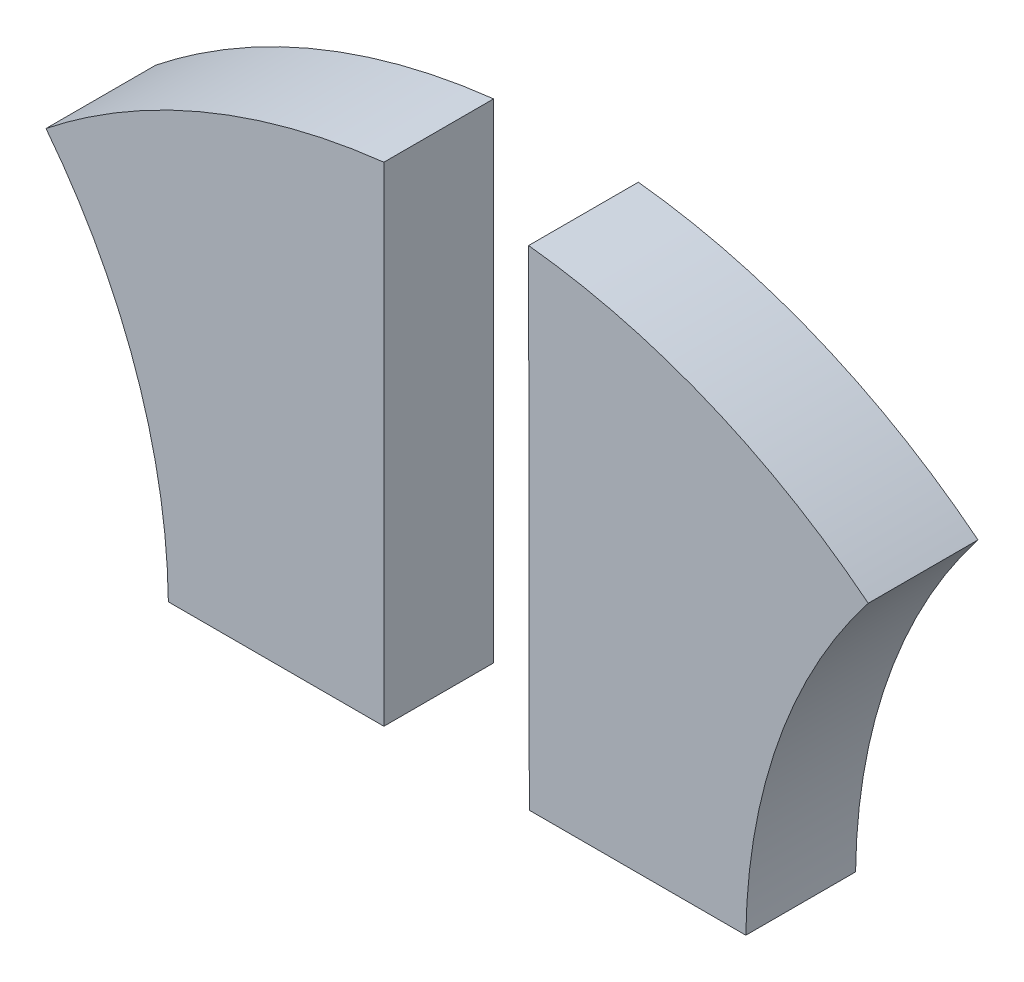
SolidWorks part; units mm, degrees
ref_plane "Alzado" through (0, 0, 0) normal (0, 0, 1) x (1, 0, 0)
ref_plane "Planta" through (0, 0, 0) normal (0, 1, 0) x (1, 0, 0)
ref_plane "Vista lateral" through (0, 0, 0) normal (1, 0, 0) x (0, 0, -1)
sketch "Model" plane through (0, 0, 0) normal (0, 0, 1) x (1, 0, 0)
  line L0 (34.3971, 11.0191) -> (28.5047, 11.0191)
  line L1 (34.3971, 24.3756) -> (34.3971, 11.0191)
  line L2 (44.2933, 11.0191) -> (38.3729, 11.0191)
  line L3 (38.3729, 11.0191) -> (38.3541, 24.3809)
  arc A0 (28.5047, 11.0191) -> (25.1591, 20.555) centre (12.6955, 10.8273) ccw
  arc A1 (47.6408, 20.5544) -> (44.2933, 11.0191) centre (60.0956, 10.8267) ccw
  ellipse E0 centre (36.3996, 6.0191) end of major axis (36.3996, -12.4491) minor radius 18.222 (34.3971, 24.3756) -> (25.1541, 20.551) ccw
  ellipse E1 centre (36.3996, 6.0191) end of major axis (36.3996, -12.4491) minor radius 18.222 (47.6459, 20.5503) -> (38.3541, 24.3809) ccw
extrude "Saliente-Extruir1" add sketch "Model" along normal blind 3 contours L1 E0 A0 L0 | A1 E1 L3 L2
